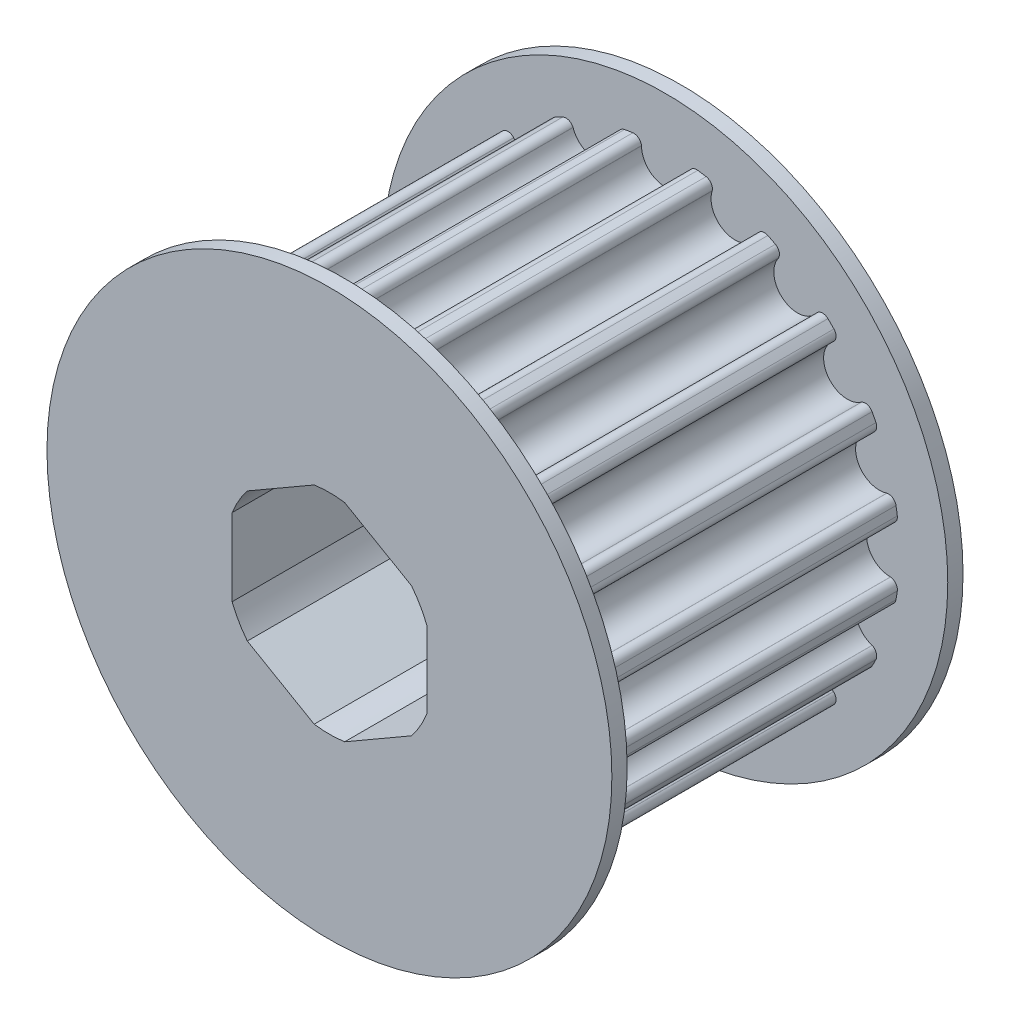
SolidWorks part; units mm, degrees
material "6061-T6 (SS)"
ref_plane "Front Plane" through (0, 0, 0) normal (0, 0, 1) x (1, 0, 0)
ref_plane "Top Plane" through (0, 0, 0) normal (0, 1, 0) x (1, 0, 0)
ref_plane "Right Plane" through (0, 0, 0) normal (1, 0, 0) x (0, 0, -1)
sketch "Pitch diameter" plane through (0, 0, 0) normal (0, 0, 1) x (1, 0, 0)
  circle A0 centre (0, 0) radius 15.9155 construction
  dimension "D1" = 31.831
sketch "Sketch2" plane through (0, 0, 0) normal (0, 0, 1) x (1, 0, 0)
  circle A0 centre (0, 0) radius 15.344
  dimension "D1" = 30.688
extrude "Boss-Extrude1" add sketch "Sketch2" along normal blind 21
sketch "Sketch3" plane through (0, 0, 0) normal (0, 0, -1) x (-1, 0, 0)
  line L0 (-1.6145, 15.2588) -> (-1.56, 14.744)
  line L1 (1.6145, 15.2588) -> (1.56, 14.744)
  line L2 (-1.56, 14.744) -> (1.56, 14.744) construction
  circle A0 centre (0, 0) radius 15.344 construction
  arc A1 (-1.56, 14.744) -> (1.56, 14.744) centre (0, 14.744) ccw
  circle A2 centre (0, 0) radius 15.344 construction
  arc A3 (1.6145, 15.2588) -> (-1.6145, 15.2588) centre (0, 0) ccw
  point P10 (0, 14.744)
  point P15 (0, 13.184)
  point P16 (0, 15.344)
  dimension "D1" = 1.56
  dimension "D2" = 2.16
extrude "Cut-Extrude1" cut sketch "Sketch3" against normal through all
fillet "Fillet1" radius 0.5 2 edges at (-1.6145, 15.2588, 10.5) (1.6145, 15.2588, 10.5)
pattern_circular "CirPattern1" count 20 over 360 about axis through (0, 0, 0) along (0, 0, 1) of "Cut-Extrude1", "Fillet1"
sketch "Sketch5" plane through (0, 0, 0) normal (0, 0, -1) x (-1, 0, 0)
  line L0 (0, 7.3617) -> (-0.9991, 6.7848) construction
  line L1 (0.9991, -6.7848) -> (5.3763, -4.2577)
  line L2 (6.3754, -2.5271) -> (6.3754, 2.5271)
  line L3 (5.3763, 4.2577) -> (0.9991, 6.7848)
  line L4 (-0.9991, 6.7848) -> (-5.3763, 4.2577)
  line L5 (-6.3754, 2.5271) -> (-6.3754, -2.5271)
  line L6 (-5.3763, -4.2577) -> (-0.9991, -6.7848)
  line L7 (0.9991, 6.7848) -> (0, 7.3617) construction
  line L8 (6.3754, 3.6808) -> (5.3763, 4.2577) construction
  line L9 (6.3754, 2.5271) -> (6.3754, 3.6808) construction
  line L10 (6.3754, -3.6808) -> (6.3754, -2.5271) construction
  line L11 (5.3763, -4.2577) -> (6.3754, -3.6808) construction
  line L12 (-0.9991, -6.7848) -> (0, -7.3617) construction
  line L13 (0, -7.3617) -> (0.9991, -6.7848) construction
  line L14 (-6.3754, -3.6808) -> (-5.3763, -4.2577) construction
  line L15 (-6.3754, -2.5271) -> (-6.3754, -3.6808) construction
  line L16 (-5.3763, 4.2577) -> (-6.3754, 3.6808) construction
  line L17 (-6.3754, 3.6808) -> (-6.3754, 2.5271) construction
  circle A1 centre (0, 0) radius 6.3754 construction
  arc A2 (-5.3763, 4.2577) -> (-6.3754, 2.5271) centre (0, 0) ccw
  arc A3 (-0.9991, 6.7848) -> (-5.3763, 4.2577) centre (0, 0) ccw construction
  arc A4 (5.3763, 4.2577) -> (0.9991, 6.7848) centre (0, 0) ccw construction
  arc A5 (0.9991, 6.7848) -> (-0.9991, 6.7848) centre (0, 0) ccw
  arc A6 (6.3754, -2.5271) -> (6.3754, 2.5271) centre (0, 0) ccw construction
  arc A7 (6.3754, 2.5271) -> (5.3763, 4.2577) centre (0, 0) ccw
  arc A8 (0.9991, -6.7848) -> (5.3763, -4.2577) centre (0, 0) ccw construction
  arc A9 (5.3763, -4.2577) -> (6.3754, -2.5271) centre (0, 0) ccw
  arc A10 (-5.3763, -4.2577) -> (-0.9991, -6.7848) centre (0, 0) ccw construction
  arc A11 (-0.9991, -6.7848) -> (0.9991, -6.7848) centre (0, 0) ccw
  arc A12 (-6.3754, 2.5271) -> (-6.3754, -2.5271) centre (0, 0) ccw construction
  arc A13 (-6.3754, -2.5271) -> (-5.3763, -4.2577) centre (0, 0) ccw
  dimension "D2" = 12.7508
  dimension "D3" = 13.716
  dimension "D1" = 12.7508
extrude "Cut-Extrude2" cut sketch "Sketch5" against normal through all contours L5 A13 L6 A11 L1 A9 L2 A7 L3 A5 L4 A2
ref_plane "Plane1" through (0, 0, 10.5) normal (0, 0, 1) x (1, 0, 0)
sketch "Sketch7" plane through (0, 0, 21) normal (0, 0, 1) x (1, 0, 0)
  line L18 (6.3754, -2.5271) -> (6.3754, 2.5271)
  line L19 (0.9991, -6.7848) -> (5.3763, -4.2577)
  line L20 (-5.3763, -4.2577) -> (-0.9991, -6.7848)
  line L21 (-6.3754, 2.5271) -> (-6.3754, -2.5271)
  line L22 (-0.9991, 6.7848) -> (-5.3763, 4.2577)
  line L23 (5.3763, 4.2577) -> (0.9991, 6.7848)
  line L24 (6.3754, -2.5271) -> (6.3754, 2.5271)
  line L25 (0.9991, -6.7848) -> (5.3763, -4.2577)
  line L26 (-5.3763, -4.2577) -> (-0.9991, -6.7848)
  line L27 (-6.3754, 2.5271) -> (-6.3754, -2.5271)
  line L28 (-0.9991, 6.7848) -> (-5.3763, 4.2577)
  line L29 (5.3763, 4.2577) -> (0.9991, 6.7848)
  circle A0 centre (0, 0) radius 18.5
  arc A7 (5.3763, -4.2577) -> (6.3754, -2.5271) centre (0, 0) ccw
  arc A8 (-0.9991, -6.7848) -> (0.9991, -6.7848) centre (0, 0) ccw
  arc A9 (-6.3754, -2.5271) -> (-5.3763, -4.2577) centre (0, 0) ccw
  arc A10 (-5.3763, 4.2577) -> (-6.3754, 2.5271) centre (0, 0) ccw
  arc A11 (0.9991, 6.7848) -> (-0.9991, 6.7848) centre (0, 0) ccw
  arc A12 (6.3754, 2.5271) -> (5.3763, 4.2577) centre (0, 0) ccw
  arc A13 (5.3763, -4.2577) -> (6.3754, -2.5271) centre (0, 0) ccw
  arc A14 (-0.9991, -6.7848) -> (0.9991, -6.7848) centre (0, 0) ccw
  arc A15 (-6.3754, -2.5271) -> (-5.3763, -4.2577) centre (0, 0) ccw
  arc A16 (-5.3763, 4.2577) -> (-6.3754, 2.5271) centre (0, 0) ccw
  arc A17 (0.9991, 6.7848) -> (-0.9991, 6.7848) centre (0, 0) ccw
  arc A18 (6.3754, 2.5271) -> (5.3763, 4.2577) centre (0, 0) ccw
  dimension "D1" = 37
  dimension "D2" = 0
extrude "Boss-Extrude2" add sketch "Sketch7" along normal blind 1
mirror "Mirror1" about plane through (0, 0, 10.5) normal (0, 0, 1) of "Boss-Extrude2"
equation "\"NumberOfTeeth\"= 20"
equation "\"Pitch\"= 5mm"
equation "\"PitchDiameter\"= ( \"Pitch\" * \"NumberOfTeeth\" ) / Pi"
equation "\"OD\"= \"PitchDiameter\" - 0.0225in * 2"
equation "\"D1@Pitch diameter\" = \"PitchDiameter\""
equation "\"D1@Sketch2\"=\"OD\""
equation "\"D1@CirPattern1\"=\"NumberOfTeeth\""
equation "\"D1@Sketch5\"=12.7mm+0.002in"
